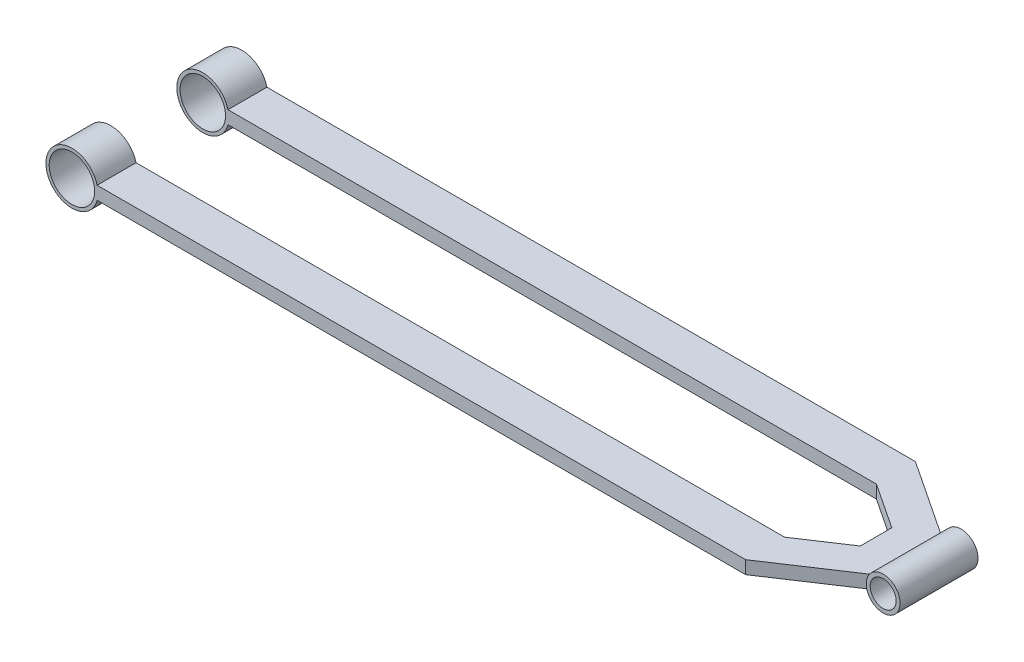
SolidWorks part; units mm, degrees
material "1060 Alloy"
ref_plane "Front Plane" through (0, 0, 0) normal (0, 0, 1) x (1, 0, 0)
ref_plane "Top Plane" through (0, 0, 0) normal (0, 1, 0) x (1, 0, 0)
ref_plane "Right Plane" through (0, 0, 0) normal (1, 0, 0) x (0, 0, -1)
ref_plane "Plane1" through (0, 0, -35.355) normal (0, 0, 1) x (1, 0, 0)
sketch "Sketch2" plane through (0, 0, -35.355) normal (0, 0, 1) x (1, 0, 0)
  circle A0 centre (0, 0) radius 20
  circle A1 centre (0, 0) radius 17.5
  dimension "D1" = 40
  dimension "D2" = 35
extrude "Boss-Extrude1" add sketch "Sketch2" against normal blind 30
ref_plane "Plane2" through (0, 0, 35.355) normal (0, 0, 1) x (1, 0, 0)
sketch "Sketch3" plane through (0, 0, 35.355) normal (0, 0, 1) x (1, 0, 0)
  circle A0 centre (0, 0) radius 20
  circle A1 centre (0, 0) radius 17.5
  circle A2 centre (0, 0) radius 17.5 construction
  circle A3 centre (0, 0) radius 20 construction
extrude "Boss-Extrude2" add sketch "Sketch3" along normal blind 30 separate body
sketch "Sketch4" plane through (0, 0, 0) normal (0, 1, 0) x (1, 0, 0)
  line L7 (-20, -65.355) -> (20, -65.355) construction
  line L8 (18.5, -65.355) -> (18.5, -35.355)
  line L9 (20, -35.355) -> (-20, -35.355) construction
  line L14 (20, 65.355) -> (-20, 65.355) construction
  line L15 (18.5, 65.355) -> (18.5, 35.355)
  line L17 (20, 35.355) -> (20, 65.355) construction
  line L18 (18.5, 65.355) -> (518.5, 65.355)
  line L19 (18.5, 35.355) -> (518.5, 35.355)
  line L20 (-20, 35.355) -> (20, 35.355) construction
  line L21 (578.5, 25.5555) -> (578.5, -25.5555)
  line L22 (518.5, -65.355) -> (578.5, -25.5555)
  line L23 (518.5, -35.355) -> (553.5, -12.1386)
  line L24 (553.5, -12.1386) -> (553.5, 12.1386)
  line L25 (553.5, 12.1386) -> (518.5, 35.355)
  line L26 (578.5, 25.5555) -> (518.5, 65.355)
  line L27 (18.5, -35.355) -> (518.5, -35.355)
  line L28 (18.5, -65.355) -> (518.5, -65.355)
  dimension "D1" = 1.5
  dimension "D2" = 500
  dimension "D3" = 25
  dimension "D4" = 25
  dimension "D5" = 500
  dimension "D6" = 60
extrude "Boss-Extrude3" add sketch "Sketch4" along normal mid plane 10
sketch "Sketch5" plane through (0, 0, 0) normal (0, 0, 1) x (1, 0, 0)
  line L0 (0, 0) -> (687.6718, 0) construction
  circle A0 centre (589, 0) radius 13
  circle A1 centre (589, 0) radius 10
  dimension "D1" = 26
  dimension "D2" = 20
  dimension "D3" = 589
extrude "Boss-Extrude4" add sketch "Sketch5" along normal mid plane 60
